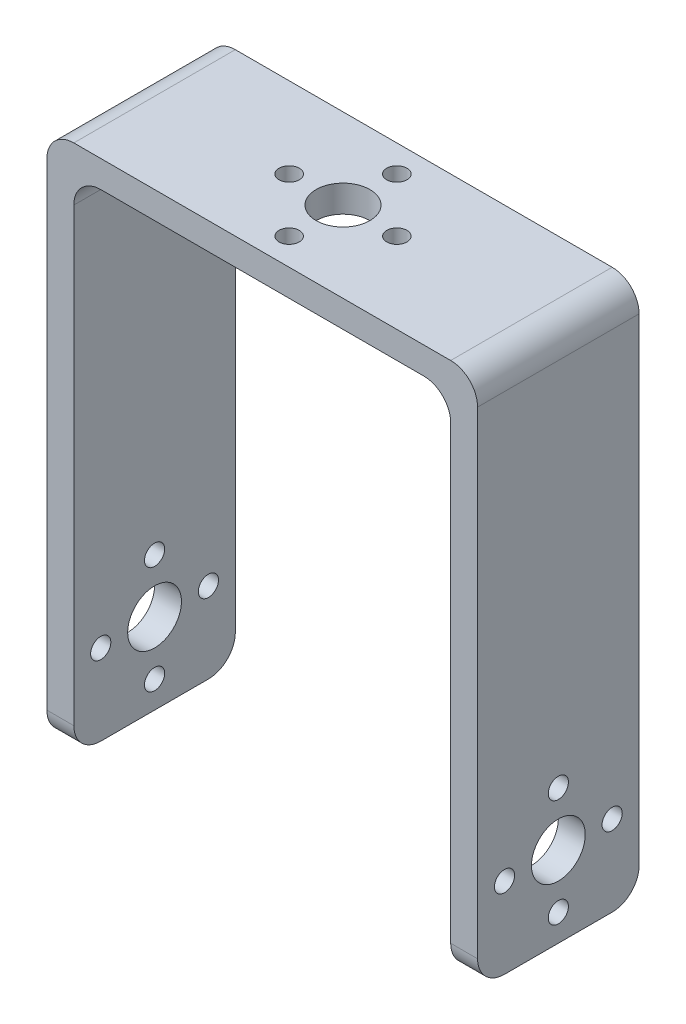
SolidWorks part; units mm, degrees
ref_plane "Front Plane" through (0, 0, 0) normal (0, 0, 1) x (1, 0, 0)
ref_plane "Top Plane" through (0, 0, 0) normal (0, 1, 0) x (1, 0, 0)
ref_plane "Right Plane" through (0, 0, 0) normal (1, 0, 0) x (0, 0, -1)
sketch "Sketch1" plane through (0, 0, 0) normal (0, 0, 1) x (1, 0, 0)
  line L0 (-35.9477, -38.738) -> (-35.9477, 36.262)
  line L1 (-35.9477, 36.262) -> (20.0523, 36.262)
  line L2 (20.0523, 36.262) -> (20.0523, -38.738)
  line L3 (-39.9477, -38.738) -> (-39.9477, 40.262)
  line L4 (-39.9477, 40.262) -> (24.0523, 40.262)
  line L5 (24.0523, 40.262) -> (24.0523, -38.738)
  line L6 (-39.9477, -38.738) -> (-35.9477, -38.738)
  line L7 (20.0523, -38.738) -> (24.0523, -38.738)
  line L8 (24.0523, -38.738) -> (23.9671, -37.3607)
  dimension "D1" = 4
extrude "Boss-Extrude1" add sketch "Sketch1" along normal blind 24
sketch "Sketch2" plane through (24.0523, 0, 0) normal (1, 0, 0) x (0, 0, -1)
  line L0 (-24, 40.262) -> (-24, -38.738) construction
  line L7 (-24, -38.738) -> (0, -38.738) construction
  circle A0 centre (-12, -26.738) radius 4
  circle A1 centre (-4, -26.738) radius 1.5
  circle A2 centre (-12, -34.738) radius 1.5
  circle A3 centre (-12, -26.738) radius 4
  circle A4 centre (-20, -26.738) radius 1.5
  circle A5 centre (-12, -26.738) radius 4
  circle A6 centre (-12, -18.738) radius 1.5
  circle A7 centre (-12, -26.738) radius 4
  point P20 (-12, -26.738)
  dimension "D1" = 12
  dimension "D2" = 12
  dimension "D3" = 4
extrude "Cut-Extrude1" cut sketch "Sketch2" against normal blind 4
sketch "Sketch3" plane through (-39.9477, 0, 0) normal (-1, 0, 0) x (0, 0, 1)
  line L0 (0, -38.738) -> (0, 40.262) construction
  line L1 (24, -38.738) -> (0, -38.738) construction
  line L2 (12, -26.738) -> (20, -26.738)
  circle A0 centre (12, -26.738) radius 4
  circle A1 centre (20, -26.738) radius 1.5
  circle A2 centre (12, -34.738) radius 1.5
  circle A3 centre (4, -26.738) radius 1.5
  circle A4 centre (12, -18.738) radius 1.5
  point P17 (12, -26.738)
  dimension "D1" = 12
  dimension "D3" = 4
  dimension "D2" = 12
extrude "Cut-Extrude2" cut sketch "Sketch3" against normal blind 4 contours A4 | A1 | A0 | A2 | A3
fillet "Fillet1" radius 4 8 edges at (22.0523, -38.738, 0) (22.0523, -38.738, 24) (-37.9477, -38.738, 0) (-37.9477, -38.738, 24) (-35.9477, 36.262, 12) (-39.9477, 40.262, 12) (20.0523, 36.262, 12) (24.0523, 40.262, 12)
sketch "Sketch6" plane through (0, 40.262, 0) normal (0, 1, 0) x (1, 0, 0)
  line L3 (-35.9477, -24) -> (20.0523, -24) construction
  line L4 (-39.9477, -20) -> (-39.9477, -4) construction
  circle A0 centre (-7.9477, -12) radius 4
  circle A1 centre (0.0523, -12) radius 1.5
  circle A2 centre (-7.9477, -20) radius 1.5
  circle A3 centre (-7.9477, -12) radius 4
  circle A4 centre (-15.9477, -12) radius 1.5
  circle A5 centre (-7.9477, -12) radius 4
  circle A6 centre (-7.9477, -4) radius 1.5
  circle A7 centre (-7.9477, -12) radius 4
  point P6 (-39.9477, -12)
  point P25 (-7.9477, -12)
  dimension "D1" = 12
  dimension "D3" = 4
  dimension "D2" = 32
extrude "Cut-Extrude3" cut sketch "Sketch6" against normal blind 4 contours A6 | A1 | A2 | A4 | A0
